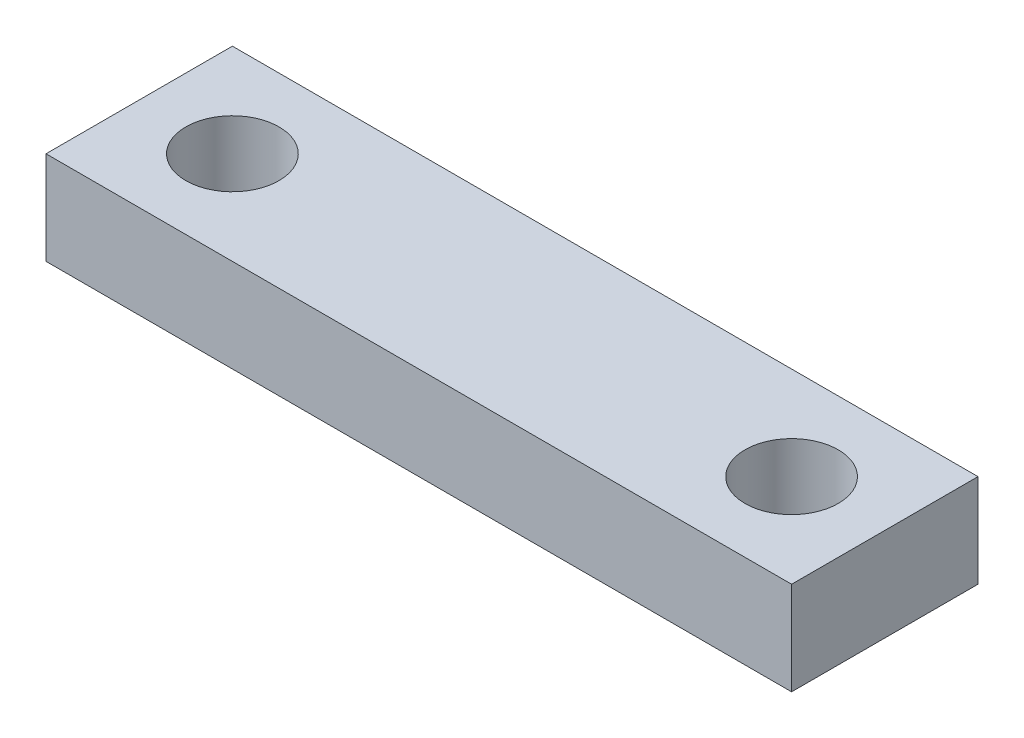
SolidWorks part; units mm, degrees
ref_plane "Front Plane" through (0, 0, 0) normal (0, 0, 1) x (1, 0, 0)
ref_plane "Top Plane" through (0, 0, 0) normal (0, 1, 0) x (1, 0, 0)
ref_plane "Right Plane" through (0, 0, 0) normal (1, 0, 0) x (0, 0, -1)
sketch "Sketch1" plane through (0, 0, 0) normal (0, 1, 0) x (1, 0, 0)
  line L1 (0, 0) -> (80, 0)
  line L2 (0, 0) -> (0, 20)
  line L3 (0, 20) -> (80, 20)
  line L4 (80, 0) -> (80, 20)
  circle A0 centre (10, 10) radius 5
  circle A1 centre (70, 10) radius 5
  point P9 (0, 10)
  dimension "D4" = 10
  dimension "D1" = 20
  dimension "D2" = 80
  dimension "D3" = 60
  dimension "D5" = 10
extrude "Boss-Extrude1" add sketch "Sketch1" along normal blind 10
